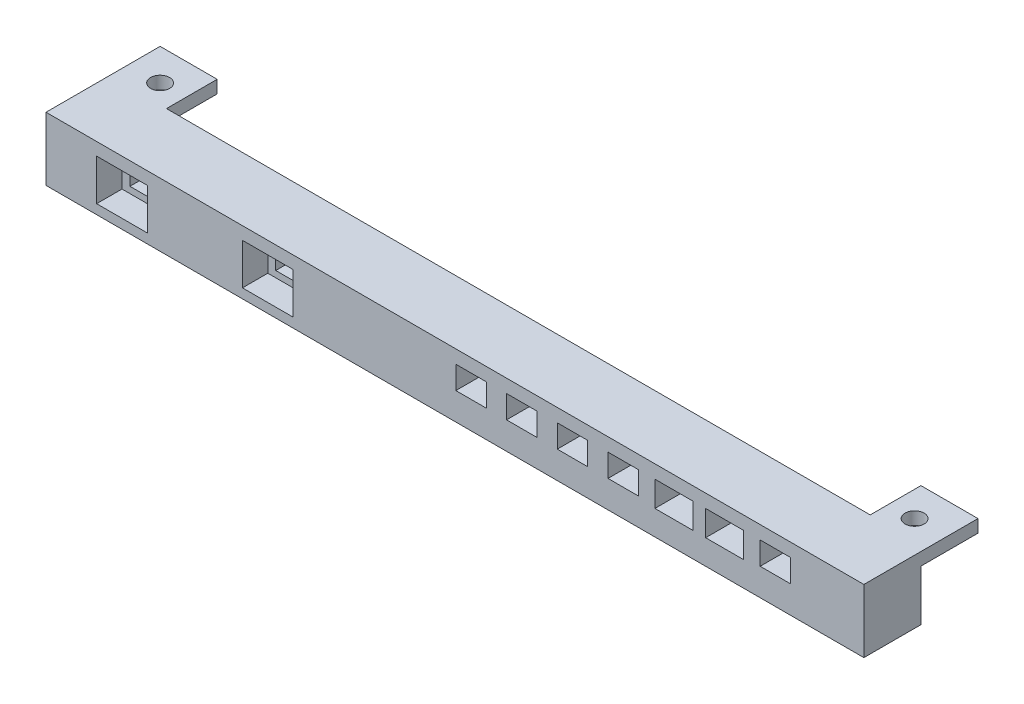
SolidWorks part; units mm, degrees
ref_plane "Front Plane" through (0, 0, 0) normal (0, 0, 1) x (1, 0, 0)
ref_plane "Top Plane" through (0, 0, 0) normal (0, 1, 0) x (1, 0, 0)
ref_plane "Right Plane" through (0, 0, 0) normal (1, 0, 0) x (0, 0, -1)
sketch "Sketch3" plane through (0, 0, 0) normal (0, 1, 0) x (1, 0, 0)
  line L0 (-59.5, 0) -> (59.5, 0) construction
  line L1 (-64.5, -13) -> (64.5, -13)
  line L2 (-64.5, 5) -> (-54.5, 5)
  line L3 (-64.5, 5) -> (-64.5, -13)
  line L5 (54.5, 5) -> (54.5, -3)
  line L6 (-64.5, 5) -> (-58.4393, -1.0607) construction
  line L7 (-64.5, -5) -> (-54.5, 5) construction
  line L8 (64.5, 5) -> (54.5, 5)
  line L9 (64.5, 5) -> (64.5, -13)
  line L10 (-54.5, 5) -> (-54.5, -3)
  line L11 (-54.5, -3) -> (54.5, -3)
  line L12 (64.5, 5) -> (58.4393, -1.0607) construction
  line L13 (64.5, -5) -> (54.5, 5) construction
  circle A0 centre (-59.5, 0) radius 1.5
  circle A1 centre (59.5, 0) radius 1.5
  point P4 (0, 0)
  dimension "D2" = 3
  dimension "D3" = 3
  dimension "D10" = 5
  dimension "D1" = 119
  dimension "D4" = 10
  dimension "D5" = 10
  dimension "D6" = 10
  dimension "D7" = 10
  dimension "D8" = 18
  dimension "D9" = 18
extrude "Boss-Extrude4" add sketch "Sketch3" along normal blind 2
sketch "Sketch8" plane through (0, 2, 0) normal (0, 1, 0) x (1, 0, 0)
  line L0 (-64.5, 5) -> (-64.5, -13) construction
  line L1 (-64.5, -4) -> (64.5, -4)
  line L2 (-64.5, -4) -> (-64.5, -13)
  line L3 (-64.5, -13) -> (64.5, -13)
  line L4 (64.5, -4) -> (64.5, -13)
extrude "Boss-Extrude5" add sketch "Sketch8" against normal blind 10
sketch "Sketch9" plane through (0, 0, 13) normal (0, 0, 1) x (1, 0, 0)
  line L1 (-55.7637, -0.5985) -> (-49.2637, -0.5985) construction
  line L2 (-55.7637, -0.5985) -> (-55.7637, -5.8985) construction
  line L3 (-55.7637, -5.8985) -> (-49.2637, -5.8985) construction
  line L4 (-49.2637, -0.5985) -> (-49.2637, -5.8985) construction
  line L5 (-32.7637, -0.5985) -> (-26.2637, -0.5985) construction
  line L6 (-32.7637, -0.5985) -> (-32.7637, -5.8985) construction
  line L7 (-32.7637, -5.8985) -> (-26.2637, -5.8985) construction
  line L8 (-26.2637, -0.5985) -> (-26.2637, -5.8985) construction
  line L9 (-64.5, 2) -> (-64.5, -8) construction
  line L10 (8.1413, -0.0985) -> (12.9413, -0.0985) construction
  line L11 (8.1413, -0.0985) -> (8.1413, -3.6985) construction
  line L12 (8.1413, -3.6985) -> (12.9413, -3.6985) construction
  line L14 (12.9413, -0.0985) -> (12.9413, -3.6985) construction
  line L15 (16.1413, -0.0985) -> (20.9413, -0.0985) construction
  line L16 (16.1413, -0.0985) -> (16.1413, -3.6985) construction
  line L17 (16.1413, -3.6985) -> (20.9413, -3.6985) construction
  line L18 (20.9413, -0.0985) -> (20.9413, -3.6985) construction
  line L19 (24.1413, -0.1006) -> (28.9413, -0.1006) construction
  line L20 (24.1413, -0.1006) -> (24.1413, -3.6985) construction
  line L21 (24.1413, -3.6985) -> (28.9413, -3.6985) construction
  line L22 (28.9413, -0.1006) -> (28.9413, -3.6985) construction
  line L23 (31.5413, -0.0985) -> (37.5413, -0.0985) construction
  line L24 (31.5413, -0.0985) -> (31.5413, -4.0985) construction
  line L25 (31.5413, -4.0985) -> (37.5413, -4.0985) construction
  line L26 (37.5413, -0.0985) -> (37.5413, -4.0985) construction
  line L27 (39.5413, -0.0985) -> (45.5413, -0.0985) construction
  line L28 (39.5413, -0.0985) -> (39.5413, -4.0985) construction
  line L29 (39.5413, -4.0985) -> (45.5413, -4.0985) construction
  line L30 (45.5413, -0.0985) -> (45.5413, -4.0985) construction
  line L31 (48.1413, -0.0985) -> (52.9413, -0.0985) construction
  line L32 (48.1413, -0.0985) -> (48.1413, -3.6985) construction
  line L33 (48.1413, -3.6985) -> (52.9413, -3.6985) construction
  line L34 (52.9413, -0.0985) -> (52.9413, -3.6985) construction
  line L35 (0.1413, -3.6985) -> (4.9413, -3.6985) construction
  line L36 (0.1413, -3.6985) -> (0.1413, -0.0985) construction
  line L37 (0.1413, -0.0985) -> (4.9413, -0.0985) construction
  line L38 (4.9413, -3.6985) -> (4.9413, -0.0985) construction
  line L39 (-64.5, 2) -> (64.5, 2) construction
  point P61 (20.9413, -1.8985)
  dimension "D1" = 8.7363
  dimension "D2" = 6.5
  dimension "D3" = 5.3
  dimension "D4" = 2.5985
  dimension "D5" = 31.7363
  dimension "D6" = 6.5
  dimension "D7" = 5.3
  dimension "D8" = 2.5985
  dimension "D9" = 4.8
  dimension "D10" = 3.6
  dimension "D11" = 2.0985
  dimension "D12" = 26.405
  dimension "D13" = 3.2
  dimension "D14" = 4.8
  dimension "D15" = 3.6
  dimension "D16" = 2.0985
  dimension "D17" = 2.0985
  dimension "D18" = 3.6
  dimension "D19" = 4.8
  dimension "D20" = 3.2
  dimension "D21" = 3.2
  dimension "D22" = 4.8
  dimension "D23" = 3.5979
  dimension "D24" = 2.1006
  dimension "D25" = 4
  dimension "D26" = 6
  dimension "D27" = 2.6
  dimension "D28" = 2.0985
  dimension "D29" = 4
  dimension "D30" = 2
  dimension "D31" = 6
  dimension "D32" = 2.0985
  dimension "D33" = 3.6
  dimension "D34" = 4.8
  dimension "D35" = 2.6
  dimension "D36" = 2.0985
sketch "Sketch10" plane through (0, 0, 13) normal (0, 0, 1) x (1, 0, 0)
  line L0 (-52.5137, -0.5985) -> (-52.5137, -5.8985) construction
  line L1 (-55.7637, -0.5985) -> (-49.2637, -0.5985) construction
  line L2 (-55.7637, -5.8985) -> (-49.2637, -5.8985) construction
  line L3 (-55.7637, -3.2485) -> (-49.2637, -3.2485) construction
  line L4 (-55.7637, -0.5985) -> (-55.7637, -5.8985) construction
  line L5 (-49.2637, -0.5985) -> (-49.2637, -5.8985) construction
  line L6 (-32.7637, -3.2485) -> (-26.2637, -3.2485) construction
  line L8 (-55.2637, -0.9985) -> (-49.7637, -0.9985)
  line L9 (-55.2637, -0.9985) -> (-55.2637, -5.4985)
  line L10 (-55.2637, -5.4985) -> (-49.7637, -5.4985)
  line L11 (-49.7637, -0.9985) -> (-49.7637, -5.4985)
  line L12 (-55.2637, -0.9985) -> (-49.7637, -5.4985) construction
  line L13 (-32.7637, -0.5985) -> (-32.7637, -5.8985) construction
  line L14 (-26.2637, -0.5985) -> (-26.2637, -5.8985) construction
  line L15 (-55.2637, -5.4985) -> (-49.7637, -0.9985) construction
  line L16 (-32.7637, -0.5985) -> (-26.2637, -0.5985) construction
  line L17 (-29.5137, -0.5985) -> (-29.5137, -5.8985) construction
  line L18 (-32.7637, -5.8985) -> (-26.2637, -5.8985) construction
  line L19 (-32.2637, -0.9985) -> (-26.7637, -0.9985)
  line L20 (-32.2637, -0.9985) -> (-32.2637, -5.4985)
  line L21 (-32.2637, -5.4985) -> (-26.7637, -5.4985)
  line L22 (-26.7637, -0.9985) -> (-26.7637, -5.4985)
  line L23 (-32.2637, -0.9985) -> (-26.7637, -5.4985) construction
  line L24 (-32.2637, -5.4985) -> (-26.7637, -0.9985) construction
  line L27 (0.1413, -0.0985) -> (4.9413, -0.0985)
  line L30 (0.1413, -0.0985) -> (0.1413, -3.6985)
  line L31 (0.1413, -3.6985) -> (4.9413, -3.6985)
  line L32 (4.9413, -0.0985) -> (4.9413, -3.6985)
  line L33 (8.1413, -0.0985) -> (12.9413, -0.0985)
  line L34 (8.1413, -0.0985) -> (8.1413, -3.6985)
  line L35 (8.1413, -3.6985) -> (12.9413, -3.6985)
  line L36 (12.9413, -0.0985) -> (12.9413, -3.6985)
  line L37 (16.1413, -0.0985) -> (20.9413, -0.0985)
  line L38 (16.1413, -0.0985) -> (16.1413, -3.6985)
  line L39 (16.1413, -3.6985) -> (20.9413, -3.6985)
  line L40 (20.9413, -0.0985) -> (20.9413, -3.6985)
  line L41 (24.1413, -0.1006) -> (28.9413, -0.1006)
  line L42 (24.1413, -0.1006) -> (24.1413, -3.6985)
  line L43 (24.1413, -3.6985) -> (28.9413, -3.6985)
  line L44 (28.9413, -0.1006) -> (28.9413, -3.6985)
  line L45 (31.5413, -0.0985) -> (37.5413, -0.0985)
  line L46 (31.5413, -0.0985) -> (31.5413, -4.0985)
  line L47 (31.5413, -4.0985) -> (37.5413, -4.0985)
  line L48 (37.5413, -0.0985) -> (37.5413, -4.0985)
  line L49 (39.5413, -0.0985) -> (45.5413, -0.0985)
  line L50 (39.5413, -0.0985) -> (39.5413, -4.0985)
  line L51 (39.5413, -4.0985) -> (45.5413, -4.0985)
  line L52 (45.5413, -0.0985) -> (45.5413, -4.0985)
  line L53 (48.1413, -0.0985) -> (52.9413, -0.0985)
  line L54 (48.1413, -0.0985) -> (48.1413, -3.6985)
  line L55 (48.1413, -3.6985) -> (52.9413, -3.6985)
  line L56 (52.9413, -0.0985) -> (52.9413, -3.6985)
  point P12 (-52.5137, -3.2485)
  point P13 (-52.5137, -3.2485)
  point P23 (-29.5137, -3.2485)
  point P31 (-29.5137, -3.2485)
  point P48 (2.5413, -1.8985)
  dimension "D1" = 4.5
  dimension "D2" = 5.5
  dimension "D3" = 4.5
  dimension "D4" = 5.5
extrude "Cut-Extrude1" cut sketch "Sketch10" against normal blind 18
sketch "Sketch11" plane through (0, 0, 13) normal (0, 0, 1) x (1, 0, 0)
  line L0 (-49.7637, -0.9985) -> (-55.2637, -0.9985) construction
  line L1 (-56.5137, 0.0015) -> (-48.5137, 0.0015)
  line L2 (-56.5137, 0.0015) -> (-56.5137, -6.4985)
  line L3 (-56.5137, -6.4985) -> (-48.5137, -6.4985)
  line L4 (-48.5137, 0.0015) -> (-48.5137, -6.4985)
  line L5 (-56.5137, 0.0015) -> (-48.5137, -6.4985) construction
  line L6 (-56.5137, -6.4985) -> (-48.5137, 0.0015) construction
  line L9 (-49.7637, -5.4985) -> (-49.7637, -0.9985) construction
  line L10 (-26.7637, -0.9985) -> (-32.2637, -0.9985) construction
  line L11 (-33.5137, 0.0015) -> (-25.5137, 0.0015)
  line L12 (-33.5137, 0.0015) -> (-33.5137, -6.4985)
  line L13 (-33.5137, -6.4985) -> (-25.5137, -6.4985)
  line L14 (-25.5137, 0.0015) -> (-25.5137, -6.4985)
  line L15 (-33.5137, 0.0015) -> (-25.5137, -6.4985) construction
  line L16 (-33.5137, -6.4985) -> (-25.5137, 0.0015) construction
  line L17 (-26.7637, -5.4985) -> (-26.7637, -0.9985) construction
  point P0 (-52.5137, -3.2485)
  point P7 (-29.5137, -3.2485)
  point P18 (-27.9058, -4.2209)
  dimension "D1" = 2.25
  dimension "D2" = 2.75
  dimension "D3" = 6.5
  dimension "D4" = 8
  dimension "D5" = 2.25
  dimension "D6" = 2.75
  dimension "D7" = 8
  dimension "D8" = 6.5
extrude "Cut-Extrude2" cut sketch "Sketch11" against normal blind 4
sketch "Sketch12" plane through (0, 2, 0) normal (0, 1, 0) x (1, 0, 0)
  line L0 (-54.5, 5) -> (-64.5, 5) construction
  line L1 (-55.5, 5) -> (55.5, 5)
  line L2 (-55.5, 5) -> (-55.5, -3)
  line L3 (-55.5, -3) -> (55.5, -3)
  line L4 (55.5, 5) -> (55.5, -3)
  line L5 (54.5, 5) -> (54.5, -3) construction
  line L6 (-54.5, -3) -> (-54.5, 5) construction
  dimension "D1" = 1
  dimension "D2" = 1
extrude "Cut-Extrude3" cut sketch "Sketch12" against normal blind 10
